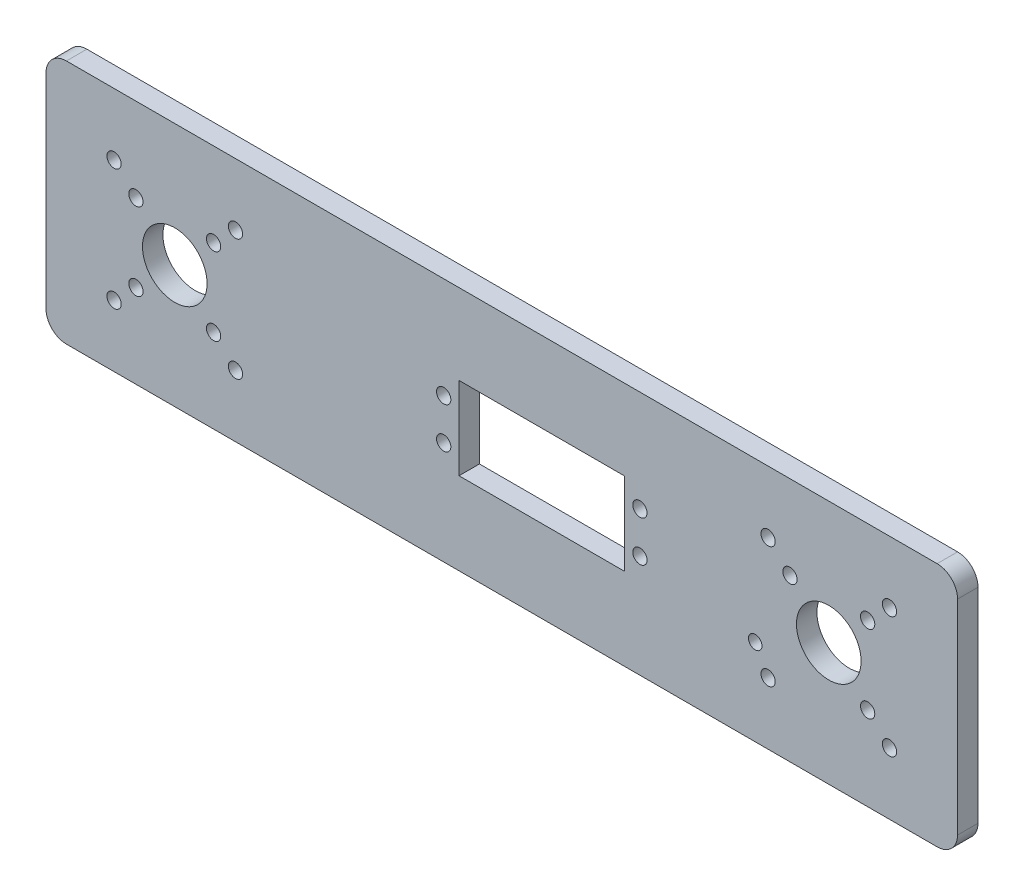
SolidWorks part; units mm, degrees
ref_plane "前视基准面" through (0, 0, 0) normal (0, 0, 1) x (1, 0, 0)
ref_plane "上视基准面" through (0, 0, 0) normal (0, 1, 0) x (1, 0, 0)
ref_plane "右视基准面" through (0, 0, 0) normal (1, 0, 0) x (0, 0, -1)
sketch "草图1" plane through (0, 0, 0) normal (0, 0, 1) x (1, 0, 0)
  line L0 (30.0389, -9.8623) -> (30.0389, 10.3377) construction
  line L1 (106.5, -30) -> (-106.5, -30)
  line L2 (111.5, -25) -> (111.5, 25)
  line L3 (106.5, 30) -> (-106.5, 30)
  line L4 (-111.5, -25) -> (-111.5, 25)
  line L5 (0, 30) -> (0, -30) construction
  line L6 (111.5, 0) -> (-111.5, 0) construction
  line L7 (30.0389, 10.3377) -> (-10.4611, 10.3377) construction
  line L8 (-10.4611, 10.3377) -> (-10.4611, -9.8623) construction
  line L9 (-10.4611, -9.8623) -> (30.0389, -9.8623) construction
  line L10 (30.0389, -9.8623) -> (30.0389, 10.3377)
  line L11 (30.0389, 10.3377) -> (-10.4611, 10.3377)
  line L12 (-10.4611, 10.3377) -> (-10.4611, -9.8623)
  line L13 (-10.4611, -9.8623) -> (30.0389, -9.8623)
  circle A0 centre (-80, 0) radius 7.905
  circle A1 centre (80, 0) radius 7.905
  arc A2 (111.5, 25) -> (106.5, 30) centre (106.5, 25) ccw
  arc A3 (106.5, -30) -> (111.5, -25) centre (106.5, -25) ccw
  arc A4 (-106.5, -30) -> (-111.5, -25) centre (-106.5, -25) cw
  arc A5 (-106.5, 30) -> (-111.5, 25) centre (-106.5, 25) ccw
  circle A6 centre (0, 0) radius 1.75 construction
  circle A7 centre (33.7889, -4.7623) radius 1.75 construction
  circle A8 centre (33.7889, 5.2377) radius 1.75 construction
  circle A9 centre (-14.2111, -4.7623) radius 1.75 construction
  circle A10 centre (-14.2111, 5.2377) radius 1.75 construction
  circle A11 centre (33.7889, -4.7623) radius 1.75
  circle A12 centre (33.7889, 5.2377) radius 1.75
  circle A13 centre (-14.2111, -4.7623) radius 1.75
  circle A14 centre (-14.2111, 5.2377) radius 1.75
  circle A15 centre (-94.8492, 14.8492) radius 1.75 construction
  circle A16 centre (-94.8492, -14.8492) radius 1.75 construction
  circle A17 centre (-65.1508, 14.8492) radius 1.75 construction
  circle A18 centre (-65.1508, -14.8492) radius 1.75 construction
  circle A19 centre (65.1508, -14.8492) radius 1.75 construction
  circle A20 centre (94.8492, -14.8492) radius 1.75 construction
  circle A21 centre (65.1508, 14.8492) radius 1.75 construction
  circle A22 centre (94.8492, 14.8492) radius 1.75 construction
  circle A23 centre (-94.8492, 14.8492) radius 1.75
  circle A24 centre (-94.8492, -14.8492) radius 1.75
  circle A25 centre (-65.1508, 14.8492) radius 1.75
  circle A26 centre (-65.1508, -14.8492) radius 1.75
  circle A27 centre (65.1508, -14.8492) radius 1.75
  circle A28 centre (94.8492, -14.8492) radius 1.75
  circle A29 centre (65.1508, 14.8492) radius 1.75
  circle A30 centre (94.8492, 14.8492) radius 1.75
  circle A31 centre (-89.5, 9.5) radius 1.75 construction
  circle A32 centre (-89.5, -9.5) radius 1.75 construction
  circle A33 centre (-70.5, 9.5) radius 1.75 construction
  circle A34 centre (-70.5, -9.5) radius 1.75 construction
  circle A35 centre (-89.5, 9.5) radius 1.75
  circle A36 centre (-89.5, -9.5) radius 1.75
  circle A37 centre (-70.5, 9.5) radius 1.75
  circle A38 centre (-70.5, -9.5) radius 1.75
  circle A39 centre (89.5, -9.5) radius 1.75 construction
  circle A40 centre (62, -8.8683) radius 1.65 construction
  circle A41 centre (70.5, 9.5) radius 1.75 construction
  circle A42 centre (89.5, 9.5) radius 1.75 construction
  circle A43 centre (89.5, -9.5) radius 1.75
  circle A44 centre (62, -8.8683) radius 1.65
  circle A45 centre (70.5, 9.5) radius 1.75
  circle A46 centre (89.5, 9.5) radius 1.75
  point P0 (0, 0)
  point P13 (111.5, 30)
  point P18 (-111.5, -30)
  point P21 (-111.5, 30)
  dimension "D3" = 15.81
  dimension "D5" = 5
  dimension "D6" = 3.5
  dimension "D1" = 60
  dimension "D2" = 223
  dimension "D4" = 160
extrude "凸台-拉伸1" add sketch "草图1" along normal blind 5
